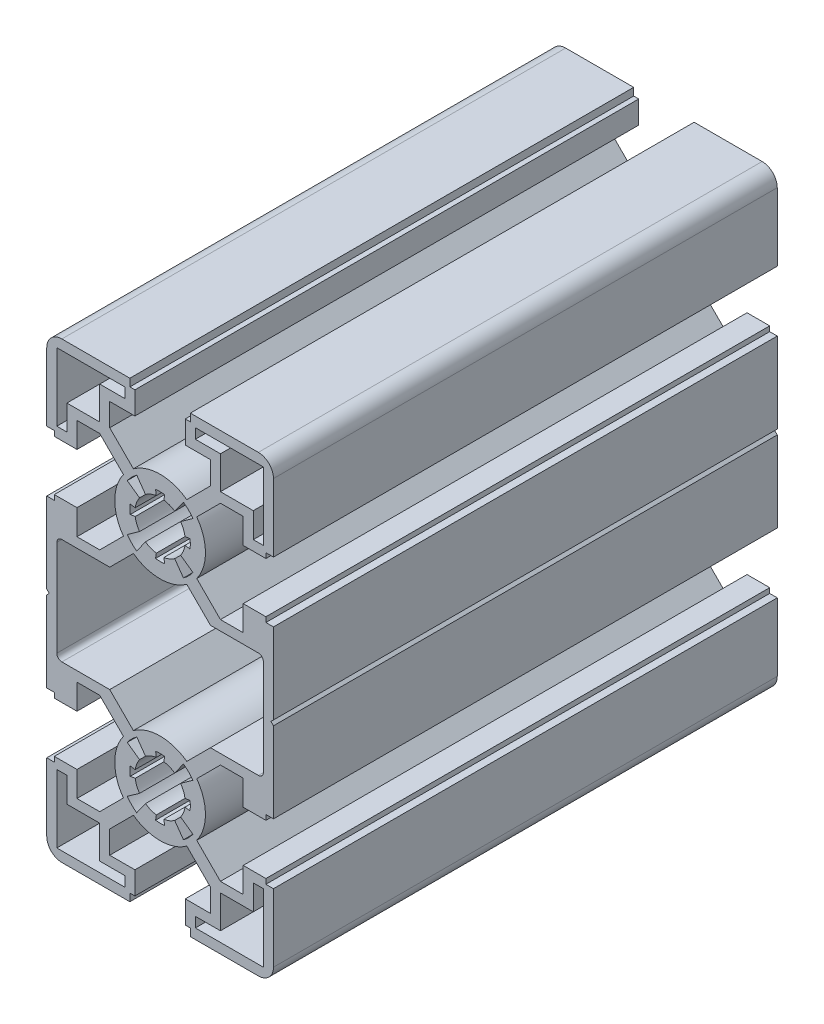
SolidWorks part; units mm, degrees
ref_plane "Ön Düzlem" through (0, 0, 0) normal (0, 0, 1) x (1, 0, 0)
ref_plane "Üst Düzlem" through (0, 0, 0) normal (0, 1, 0) x (1, 0, 0)
ref_plane "Sağ Düzlem" through (0, 0, 0) normal (1, 0, 0) x (0, 0, -1)
ref_plane "Düzlem1" through (0, 0, 100) normal (0, 0, 1) x (1, 0, 0)
sketch "Çizim1" plane through (0, 0, 100) normal (0, 0, 1) x (1, 0, 0)
  line L0 (-0.8993, -28.4322) -> (-0.7494, -27.4435)
  line L1 (-2.8971, -26.5751) -> (-4.6354, -29.0202)
  line L2 (-6.5202, -27.1354) -> (-4.0751, -25.3971)
  line L3 (-4.9435, -23.2494) -> (-5.9322, -23.3993)
  line L4 (-5.9322, -21.6007) -> (-4.9435, -21.7506)
  line L5 (-4.0751, -19.6029) -> (-6.5202, -17.8646)
  line L6 (-4.6354, -15.9798) -> (-2.8971, -18.4249)
  line L7 (-0.7494, -17.5565) -> (-0.8993, -16.5678)
  line L8 (0.8993, -16.5678) -> (0.7494, -17.5565)
  line L9 (2.8971, -18.4249) -> (4.6354, -15.9798)
  line L10 (6.5202, -17.8646) -> (4.0751, -19.6029)
  line L11 (4.9435, -21.7506) -> (5.9322, -21.6007)
  line L12 (5.9322, -23.3993) -> (4.9435, -23.2494)
  line L13 (4.0751, -25.3971) -> (6.5202, -27.1354)
  line L14 (4.6354, -29.0202) -> (2.8971, -26.5751)
  line L15 (0.7494, -27.4435) -> (0.8993, -28.4322)
  line L16 (19.5, 45) -> (6, 45)
  line L17 (6, 45) -> (6, 43.5)
  line L18 (6, 43.5) -> (5, 43.5)
  line L19 (5, 43.5) -> (5, 39)
  line L20 (5, 39) -> (10, 39)
  line L21 (10, 39) -> (10, 34.4799)
  line L22 (10, 34.4799) -> (5.2965, 29.7764)
  line L23 (-5.2965, 29.7764) -> (-10, 34.4799)
  line L24 (-10, 34.4799) -> (-10, 39)
  line L25 (-10, 39) -> (-5, 39)
  line L26 (-5, 39) -> (-5, 43.5)
  line L27 (-5, 43.5) -> (-6, 43.5)
  line L28 (-6, 43.5) -> (-6, 45)
  line L29 (-6, 45) -> (-19.5, 45)
  line L30 (-22.5, 42) -> (-22.5, 28.5)
  line L31 (-22.5, 28.5) -> (-21, 28.5)
  line L32 (-21, 28.5) -> (-21, 27.5)
  line L33 (-21, 27.5) -> (-16.5, 27.5)
  line L34 (-16.5, 27.5) -> (-16.5, 32.5)
  line L35 (-16.5, 32.5) -> (-11.9799, 32.5)
  line L36 (-11.9799, 32.5) -> (-7.2764, 27.7965)
  line L37 (-7.2764, 17.2035) -> (-11.9799, 12.5)
  line L38 (-11.9799, 12.5) -> (-16.5, 12.5)
  line L39 (-16.5, 12.5) -> (-16.5, 17.5)
  line L40 (-16.5, 17.5) -> (-21, 17.5)
  line L41 (-21, 17.5) -> (-21, 16.5)
  line L42 (-21, 16.5) -> (-22.5, 16.5)
  line L43 (-22.5, 16.5) -> (-22.5, 0.5)
  line L44 (-22.5, 0.5) -> (-22, 0)
  line L45 (-22, 0) -> (-22.5, -0.5)
  line L46 (-22.5, -0.5) -> (-22.5, -16.5)
  line L47 (-22.5, -16.5) -> (-21, -16.5)
  line L48 (-21, -16.5) -> (-21, -17.5)
  line L49 (-21, -17.5) -> (-16.5, -17.5)
  line L50 (-16.5, -17.5) -> (-16.5, -12.5)
  line L51 (-16.5, -12.5) -> (-11.9799, -12.5)
  line L52 (-11.9799, -12.5) -> (-7.2764, -17.2035)
  line L53 (-7.2764, -27.7965) -> (-11.9799, -32.5)
  line L54 (-11.9799, -32.5) -> (-16.5, -32.5)
  line L55 (-16.5, -32.5) -> (-16.5, -27.5)
  line L56 (-16.5, -27.5) -> (-21, -27.5)
  line L57 (-21, -27.5) -> (-21, -28.5)
  line L58 (-21, -28.5) -> (-22.5, -28.5)
  line L59 (-22.5, -28.5) -> (-22.5, -42)
  line L60 (-19.5, -45) -> (-6, -45)
  line L61 (-6, -45) -> (-6, -43.5)
  line L62 (-6, -43.5) -> (-5, -43.5)
  line L63 (-5, -43.5) -> (-5, -39)
  line L64 (-5, -39) -> (-10, -39)
  line L65 (-10, -39) -> (-10, -34.4799)
  line L66 (-10, -34.4799) -> (-5.2965, -29.7764)
  line L67 (5.2965, -29.7764) -> (10, -34.4799)
  line L68 (10, -34.4799) -> (10, -39)
  line L69 (10, -39) -> (5, -39)
  line L70 (5, -39) -> (5, -43.5)
  line L71 (5, -43.5) -> (6, -43.5)
  line L72 (6, -43.5) -> (6, -45)
  line L73 (6, -45) -> (19.5, -45)
  line L74 (22.5, -42) -> (22.5, -28.5)
  line L75 (22.5, -28.5) -> (21, -28.5)
  line L76 (21, -28.5) -> (21, -27.5)
  line L77 (21, -27.5) -> (16.5, -27.5)
  line L78 (16.5, -27.5) -> (16.5, -32.5)
  line L79 (16.5, -32.5) -> (11.9799, -32.5)
  line L80 (11.9799, -32.5) -> (7.2764, -27.7965)
  line L81 (7.2764, -17.2035) -> (11.9799, -12.5)
  line L82 (11.9799, -12.5) -> (16.5, -12.5)
  line L83 (16.5, -12.5) -> (16.5, -17.5)
  line L84 (16.5, -17.5) -> (21, -17.5)
  line L85 (21, -17.5) -> (21, -16.5)
  line L86 (21, -16.5) -> (22.5, -16.5)
  line L87 (22.5, -16.5) -> (22.5, -0.5)
  line L88 (22.5, -0.5) -> (22, 0)
  line L89 (22, 0) -> (22.5, 0.5)
  line L90 (22.5, 0.5) -> (22.5, 16.5)
  line L91 (22.5, 16.5) -> (21, 16.5)
  line L92 (21, 16.5) -> (21, 17.5)
  line L93 (21, 17.5) -> (16.5, 17.5)
  line L94 (16.5, 17.5) -> (16.5, 12.5)
  line L95 (16.5, 12.5) -> (11.9799, 12.5)
  line L96 (11.9799, 12.5) -> (7.2764, 17.2035)
  line L97 (7.2764, 27.7965) -> (11.9799, 32.5)
  line L98 (11.9799, 32.5) -> (16.5, 32.5)
  line L99 (16.5, 32.5) -> (16.5, 27.5)
  line L100 (16.5, 27.5) -> (21, 27.5)
  line L101 (21, 27.5) -> (21, 28.5)
  line L102 (21, 28.5) -> (22.5, 28.5)
  line L103 (22.5, 28.5) -> (22.5, 42)
  line L104 (-18.5001, 29.5001) -> (-20.5001, 29.5001)
  line L105 (-20.5001, 29.5001) -> (-20.5001, 43.0001)
  line L106 (-20.5001, 43.0001) -> (-7.0001, 43.0001)
  line L107 (-7.0001, 43.0001) -> (-7.0001, 41.0001)
  line L108 (-7.0001, 41.0001) -> (-11.98, 41.0001)
  line L109 (-11.98, 41.0001) -> (-11.98, 34.48)
  line L110 (-11.98, 34.48) -> (-18.5001, 34.48)
  line L111 (-18.5001, 34.48) -> (-18.5001, 29.5001)
  line L112 (18.5001, -29.5001) -> (20.5001, -29.5001)
  line L113 (20.5001, -29.5001) -> (20.5001, -43.0001)
  line L114 (20.5001, -43.0001) -> (7.0001, -43.0001)
  line L115 (7.0001, -43.0001) -> (7.0001, -41.0001)
  line L116 (7.0001, -41.0001) -> (11.98, -41.0001)
  line L117 (11.98, -41.0001) -> (11.98, -34.48)
  line L118 (11.98, -34.48) -> (18.5001, -34.48)
  line L119 (18.5001, -34.48) -> (18.5001, -29.5001)
  line L120 (7.0001, 41.0001) -> (7.0001, 43.0001)
  line L121 (7.0001, 43.0001) -> (20.5001, 43.0001)
  line L122 (20.5001, 43.0001) -> (20.5001, 29.5001)
  line L123 (20.5001, 29.5001) -> (18.5001, 29.5001)
  line L124 (18.5001, 29.5001) -> (18.5001, 34.48)
  line L125 (18.5001, 34.48) -> (11.98, 34.48)
  line L126 (11.98, 34.48) -> (11.98, 41.0001)
  line L127 (11.98, 41.0001) -> (7.0001, 41.0001)
  line L128 (-7.0001, -41.0001) -> (-7.0001, -43.0001)
  line L129 (-7.0001, -43.0001) -> (-20.5001, -43.0001)
  line L130 (-20.5001, -43.0001) -> (-20.5001, -29.5001)
  line L131 (-20.5001, -29.5001) -> (-18.5001, -29.5001)
  line L132 (-18.5001, -29.5001) -> (-18.5001, -34.48)
  line L133 (-18.5001, -34.48) -> (-11.98, -34.48)
  line L134 (-11.98, -34.48) -> (-11.98, -41.0001)
  line L135 (-11.98, -41.0001) -> (-7.0001, -41.0001)
  line L136 (-20.5, -9.5201) -> (-20.5, 9.5201)
  line L137 (-19.5, 10.5201) -> (-10, 10.5201)
  line L138 (-10, 10.5201) -> (-5.2965, 15.2236)
  line L139 (5.2965, 15.2236) -> (10, 10.5201)
  line L140 (10, 10.5201) -> (19.5, 10.5201)
  line L141 (20.5, 9.5201) -> (20.5, -9.5201)
  line L142 (19.5, -10.5201) -> (10, -10.5201)
  line L143 (10, -10.5201) -> (5.2965, -15.2236)
  line L144 (-5.2965, -15.2236) -> (-10, -10.5201)
  line L145 (-10, -10.5201) -> (-19.5, -10.5201)
  line L146 (-0.8993, 16.5678) -> (-0.7494, 17.5565)
  line L147 (-2.8971, 18.4249) -> (-4.6354, 15.9798)
  line L148 (-6.5202, 17.8646) -> (-4.0751, 19.6029)
  line L149 (-4.9435, 21.7506) -> (-5.9322, 21.6007)
  line L150 (-5.9322, 23.3993) -> (-4.9435, 23.2494)
  line L151 (-4.0751, 25.3971) -> (-6.5202, 27.1354)
  line L152 (-4.6354, 29.0202) -> (-2.8971, 26.5751)
  line L153 (-0.7494, 27.4435) -> (-0.8993, 28.4322)
  line L154 (0.8993, 28.4322) -> (0.7494, 27.4435)
  line L155 (2.8971, 26.5751) -> (4.6354, 29.0202)
  line L156 (6.5202, 27.1354) -> (4.0751, 25.3971)
  line L157 (4.9435, 23.2494) -> (5.9322, 23.3993)
  line L158 (5.9322, 21.6007) -> (4.9435, 21.7506)
  line L159 (4.0751, 19.6029) -> (6.5202, 17.8646)
  line L160 (4.6354, 15.9798) -> (2.8971, 18.4249)
  line L161 (0.7494, 17.5565) -> (0.8993, 16.5678)
  arc A0 (0.8993, -28.4322) -> (-0.8993, -28.4322) centre (0, -22.5) cw
  arc A1 (-0.7494, -27.4435) -> (-2.8971, -26.5751) centre (0, -22.5) cw
  arc A2 (-4.6354, -29.0202) -> (-6.5202, -27.1354) centre (0, -22.5) cw
  arc A3 (-4.0751, -25.3971) -> (-4.9435, -23.2494) centre (0, -22.5) cw
  arc A4 (-5.9322, -23.3993) -> (-5.9322, -21.6007) centre (0, -22.5) cw
  arc A5 (-4.9435, -21.7506) -> (-4.0751, -19.6029) centre (0, -22.5) cw
  arc A6 (-6.5202, -17.8646) -> (-4.6354, -15.9798) centre (0, -22.5) cw
  arc A7 (-2.8971, -18.4249) -> (-0.7494, -17.5565) centre (0, -22.5) cw
  arc A8 (-0.8993, -16.5678) -> (0.8993, -16.5678) centre (0, -22.5) cw
  arc A9 (0.7494, -17.5565) -> (2.8971, -18.4249) centre (0, -22.5) cw
  arc A10 (4.6354, -15.9798) -> (6.5202, -17.8646) centre (0, -22.5) cw
  arc A11 (4.0751, -19.6029) -> (4.9435, -21.7506) centre (0, -22.5) cw
  arc A12 (5.9322, -21.6007) -> (5.9322, -23.3993) centre (0, -22.5) cw
  arc A13 (4.9435, -23.2494) -> (4.0751, -25.3971) centre (0, -22.5) cw
  arc A14 (6.5202, -27.1354) -> (4.6354, -29.0202) centre (0, -22.5) cw
  arc A15 (2.8971, -26.5751) -> (0.7494, -27.4435) centre (0, -22.5) cw
  arc A16 (5.2965, 29.7764) -> (-5.2965, 29.7764) centre (0, 22.5) ccw
  arc A17 (-19.5, 45) -> (-22.5, 42) centre (-19.5, 42) ccw
  arc A18 (-7.2764, 27.7965) -> (-7.2764, 17.2035) centre (0, 22.5) ccw
  arc A19 (-7.2764, -17.2035) -> (-7.2764, -27.7965) centre (0, -22.5) ccw
  arc A20 (-22.5, -42) -> (-19.5, -45) centre (-19.5, -42) ccw
  arc A21 (-5.2965, -29.7764) -> (5.2965, -29.7764) centre (0, -22.5) ccw
  arc A22 (19.5, -45) -> (22.5, -42) centre (19.5, -42) ccw
  arc A23 (7.2764, -27.7965) -> (7.2764, -17.2035) centre (0, -22.5) ccw
  arc A24 (7.2764, 17.2035) -> (7.2764, 27.7965) centre (0, 22.5) ccw
  arc A25 (22.5, 42) -> (19.5, 45) centre (19.5, 42) ccw
  arc A26 (-20.5, 9.5201) -> (-19.5, 10.5201) centre (-19.5, 9.5201) cw
  arc A27 (-5.2965, 15.2236) -> (5.2965, 15.2236) centre (0, 22.5) ccw
  arc A28 (19.5, 10.5201) -> (20.5, 9.5201) centre (19.5, 9.5201) cw
  arc A29 (20.5, -9.5201) -> (19.5, -10.5201) centre (19.5, -9.5201) cw
  arc A30 (5.2965, -15.2236) -> (-5.2965, -15.2236) centre (0, -22.5) ccw
  arc A31 (-19.5, -10.5201) -> (-20.5, -9.5201) centre (-19.5, -9.5201) cw
  arc A32 (0.8993, 16.5678) -> (-0.8993, 16.5678) centre (0, 22.5) cw
  arc A33 (-0.7494, 17.5565) -> (-2.8971, 18.4249) centre (0, 22.5) cw
  arc A34 (-4.6354, 15.9798) -> (-6.5202, 17.8646) centre (0, 22.5) cw
  arc A35 (-4.0751, 19.6029) -> (-4.9435, 21.7506) centre (0, 22.5) cw
  arc A36 (-5.9322, 21.6007) -> (-5.9322, 23.3993) centre (0, 22.5) cw
  arc A37 (-4.9435, 23.2494) -> (-4.0751, 25.3971) centre (0, 22.5) cw
  arc A38 (-6.5202, 27.1354) -> (-4.6354, 29.0202) centre (0, 22.5) cw
  arc A39 (-2.8971, 26.5751) -> (-0.7494, 27.4435) centre (0, 22.5) cw
  arc A40 (-0.8993, 28.4322) -> (0.8993, 28.4322) centre (0, 22.5) cw
  arc A41 (0.7494, 27.4435) -> (2.8971, 26.5751) centre (0, 22.5) cw
  arc A42 (4.6354, 29.0202) -> (6.5202, 27.1354) centre (0, 22.5) cw
  arc A43 (4.0751, 25.3971) -> (4.9435, 23.2494) centre (0, 22.5) cw
  arc A44 (5.9322, 23.3993) -> (5.9322, 21.6007) centre (0, 22.5) cw
  arc A45 (4.9435, 21.7506) -> (4.0751, 19.6029) centre (0, 22.5) cw
  arc A46 (6.5202, 17.8646) -> (4.6354, 15.9798) centre (0, 22.5) cw
  arc A47 (2.8971, 18.4249) -> (0.7494, 17.5565) centre (0, 22.5) cw
extrude "Yükseklik-Ekstrüzyon1" add sketch "Çizim1" against normal blind 100
